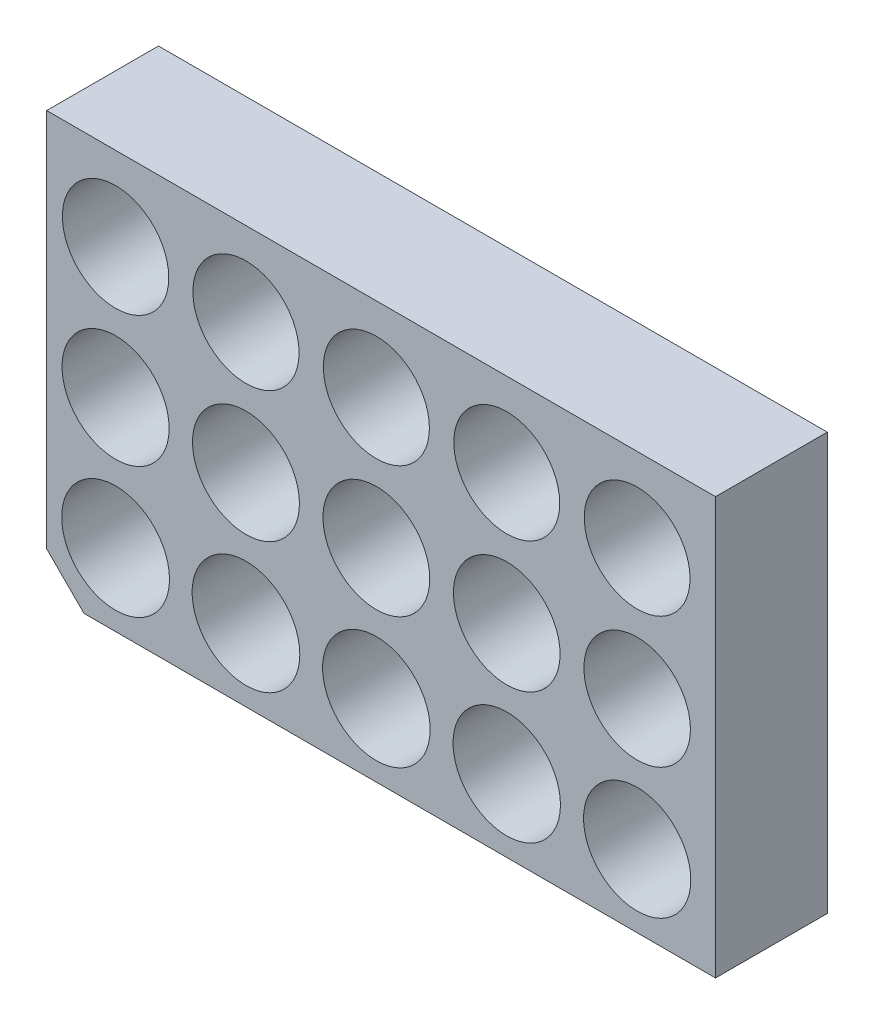
SolidWorks part; units mm, degrees
ref_plane "Front Plane" through (0, 0, 0) normal (0, 0, 1) x (1, 0, 0)
ref_plane "Top Plane" through (0, 0, 0) normal (0, 1, 0) x (1, 0, 0)
ref_plane "Right Plane" through (0, 0, 0) normal (1, 0, 0) x (0, 0, -1)
sketch "Sketch1" plane through (0, 0, 0) normal (0, 0, 1) x (1, 0, 0)
  line L3 (4.6947, 4.9344) -> (4.6947, 0) construction
  line L4 (0, 0) -> (45.5966, 0)
  line L5 (0, 0) -> (0, 28.4187)
  line L6 (0, 28.4187) -> (45.5966, 28.4187)
  line L7 (45.5966, 0) -> (45.5966, 28.4187)
  line L8 (4.6947, 4.9344) -> (0, 4.9344) construction
  circle A2 centre (4.6947, 4.9344) radius 3.675
  circle A3 centre (13.5847, 4.9344) radius 3.67
  circle A4 centre (22.4747, 4.9344) radius 3.665
  circle A5 centre (31.3647, 4.9344) radius 3.66
  circle A6 centre (40.2547, 4.9344) radius 3.655
  circle A7 centre (13.5847, 13.8244) radius 3.645
  circle A8 centre (22.4747, 13.8244) radius 3.64
  circle A9 centre (31.3647, 13.8244) radius 3.635
  circle A10 centre (40.2547, 13.8244) radius 3.63
  circle A11 centre (13.5847, 22.7144) radius 3.62
  circle A12 centre (22.4747, 22.7144) radius 3.615
  circle A13 centre (31.3647, 22.7144) radius 3.61
  circle A14 centre (40.2547, 22.7144) radius 3.605
  circle A15 centre (4.6947, 13.8244) radius 3.65
  circle A16 centre (4.6947, 22.7144) radius 3.625
  dimension "D1" = 7.35
  dimension "D2" = 7.34
  dimension "D3" = 7.33
  dimension "D4" = 7.32
  dimension "D5" = 7.31
  dimension "D6" = 7.3
  dimension "D7" = 7.29
  dimension "D8" = 7.28
  dimension "D9" = 7.27
  dimension "D10" = 7.26
  dimension "D11" = 7.25
  dimension "D12" = 7.24
  dimension "D13" = 7.23
  dimension "D14" = 7.22
  dimension "D15" = 7.21
extrude "Boss-Extrude1" add sketch "Sketch1" along normal blind 7.62
chamfer "Chamfer1" distance 2.54 angle 45 1 edges at (0, 0, 3.81)
